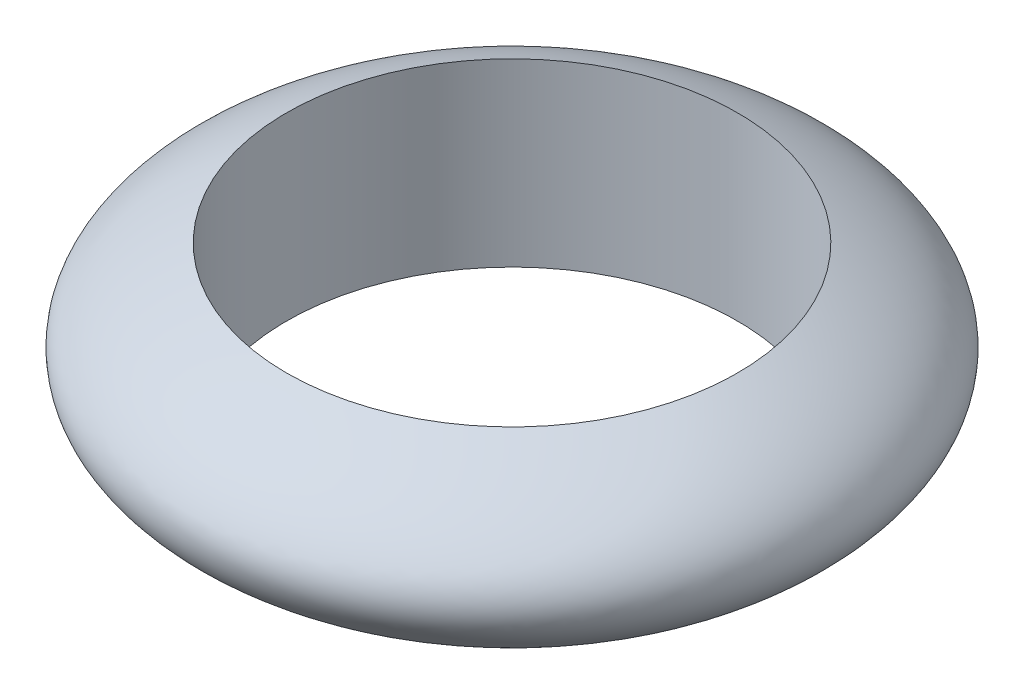
SolidWorks part; units mm, degrees
ref_plane "前视基准面" through (0, 0, 0) normal (0, 0, 1) x (1, 0, 0)
ref_plane "上视基准面" through (0, 0, 0) normal (0, 1, 0) x (1, 0, 0)
ref_plane "右视基准面" through (0, 0, 0) normal (1, 0, 0) x (0, 0, -1)
sketch "草图1" plane through (0, 0, 0) normal (0, 0, 1) x (1, 0, 0)
  line L0 (0, 36.1029) -> (0, -22.5735) construction
  line L1 (0, 10.4412) -> (0, 0.4412)
  line L2 (0, 0.4412) -> (-12.5, 0.4412)
  line L3 (-12.5, 0.4412) -> (-12.5, 10.4412)
  line L4 (-12.5, 10.4412) -> (0, 10.4412)
  spline S0 degree 2 poles (-12.5, 10.4412) (-24.0441, 5.4412) (-12.5, 0.4412) knots 0 0 0 1 1 1
  dimension "D1" = 10
  dimension "D2" = 12.5
revolve "旋转1" add sketch "草图1" angle 360 about L0
